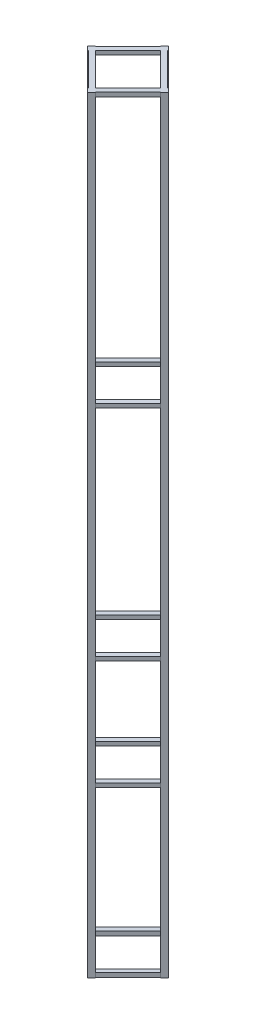
SolidWorks part; units mm, degrees
material "7075-T6 (SN)"
ref_plane "Front Plane" through (0, 0, 0) normal (0, 0, 1) x (1, 0, 0)
ref_plane "Top Plane" through (0, 0, 0) normal (0, 1, 0) x (1, 0, 0)
ref_plane "Right Plane" through (0, 0, 0) normal (1, 0, 0) x (0, 0, -1)
sketch "Sketch2" plane through (0, 0, 0) normal (0, 1, 0) x (1, 0, 0)
  line L0 (0, 93.5537) -> (-8.9803, 84.5734)
  line L1 (-8.9803, 84.5734) -> (-7.8577, 83.4509)
  line L2 (-7.8577, 83.4509) -> (0, 91.3086)
  line L3 (0, 91.3086) -> (7.8577, 83.4509)
  line L4 (7.8577, 83.4509) -> (8.9803, 84.5734)
  line L5 (8.9803, 84.5734) -> (0, 93.5537)
  line L6 (0, 0) -> (0, 186.644) construction
  line L7 (93.5537, 0) -> (84.5734, 8.9803)
  line L8 (84.5734, 8.9803) -> (83.4509, 7.8577)
  line L9 (83.4509, 7.8577) -> (91.3086, 0)
  line L10 (91.3086, 0) -> (83.4509, -7.8577)
  line L11 (83.4509, -7.8577) -> (84.5734, -8.9803)
  line L12 (84.5734, -8.9803) -> (93.5537, 0)
  line L13 (0, -93.5537) -> (8.9803, -84.5734)
  line L14 (8.9803, -84.5734) -> (7.8577, -83.4509)
  line L15 (7.8577, -83.4509) -> (0, -91.3086)
  line L16 (0, -91.3086) -> (-7.8577, -83.4509)
  line L17 (-7.8577, -83.4509) -> (-8.9803, -84.5734)
  line L18 (-8.9803, -84.5734) -> (0, -93.5537)
  line L19 (-93.5537, 0) -> (-84.5734, -8.9803)
  line L20 (-84.5734, -8.9803) -> (-83.4509, -7.8577)
  line L21 (-83.4509, -7.8577) -> (-91.3086, 0)
  line L22 (-91.3086, 0) -> (-83.4509, 7.8577)
  line L23 (-83.4509, 7.8577) -> (-84.5734, 8.9803)
  line L24 (-84.5734, 8.9803) -> (-93.5537, 0)
  point P31 (0, 0)
  dimension "D2" = 12.7
  dimension "D3" = 12.7
  dimension "D4" = 1.5875
  dimension "D5" = 1.5875
extrude "Boss-Extrude6" add sketch "Sketch2" along normal blind 1778
sketch "Sketch11" plane through (-45.6543, 0, -45.6543) normal (0.7071, 0, 0.7071) x (0.7071, 0, -0.7071)
  line L0 (-53.4524, 1778) -> (-53.4524, 0) construction
  line L1 (-64.5649, 0) -> (-53.4524, 0)
  line L2 (-64.5649, 0) -> (-64.5649, 9.525)
  line L3 (-64.5649, 9.525) -> (-53.4524, 9.525)
  line L4 (-53.4524, 0) -> (-53.4524, 9.525)
  dimension "D1" = 9.525
extrude "Boss-Extrude11" add sketch "Sketch11" along normal up to next (129.1299 mm away)
sketch "Sketch13" plane through (-37.7966, 0, 37.7966) normal (0.7071, 0, -0.7071) x (-0.7071, 0, -0.7071)
  line L0 (-66.1524, 0) -> (66.1524, 0) construction
  line L1 (-64.5649, 9.525) -> (-53.4524, 9.525)
  line L2 (-64.5649, 9.525) -> (-64.5649, 0)
  line L3 (-64.5649, 0) -> (-53.4524, 0)
  line L4 (-53.4524, 9.525) -> (-53.4524, 0)
  dimension "D1" = 11.1125
extrude "Boss-Extrude13" add sketch "Sketch13" along normal up to next (118.0174 mm away)
sketch "Sketch14" plane through (37.7966, 0, 37.7966) normal (-0.7071, 0, -0.7071) x (-0.7071, 0, 0.7071)
  line L0 (-66.1524, 0) -> (53.4524, 0) construction
  line L1 (-64.5649, 9.525) -> (-53.4524, 9.525)
  line L2 (-64.5649, 9.525) -> (-64.5649, 0)
  line L3 (-64.5649, 0) -> (-53.4524, 0)
  line L4 (-53.4524, 9.525) -> (-53.4524, 0)
  dimension "D1" = 11.1125
extrude "Boss-Extrude14" add sketch "Sketch14" along normal up to next (119.6049 mm away)
sketch "Sketch15" plane through (37.7966, 0, -37.7966) normal (-0.7071, 0, 0.7071) x (0.7071, 0, 0.7071)
  line L0 (-66.1524, 0) -> (53.4524, 0) construction
  line L1 (-64.5649, 9.525) -> (-53.4524, 9.525)
  line L2 (-64.5649, 9.525) -> (-64.5649, 0)
  line L3 (-64.5649, 0) -> (-53.4524, 0)
  line L4 (-53.4524, 9.525) -> (-53.4524, 0)
  dimension "D1" = 11.1125
extrude "Boss-Extrude15" add sketch "Sketch15" along normal up to next (106.9049 mm away)
pattern_linear "LPattern1" count 2 spacing 381 along (0, 1, 0) of "Boss-Extrude15", "Boss-Extrude14", "Boss-Extrude11", "Boss-Extrude13"
pattern_linear "LPattern2" count 2 spacing 635 along (0, 1, 0) of "Boss-Extrude15", "Boss-Extrude14", "Boss-Extrude13", "Boss-Extrude11"
pattern_linear "LPattern3" count 2 spacing 1143 along (0, 1, 0) of "Boss-Extrude11", "Boss-Extrude13", "Boss-Extrude14", "Boss-Extrude15"
pattern_linear "LPattern4" count 2 spacing 1768.475 along (0, 1, 0) of "Boss-Extrude15", "Boss-Extrude14", "Boss-Extrude13", "Boss-Extrude11"
